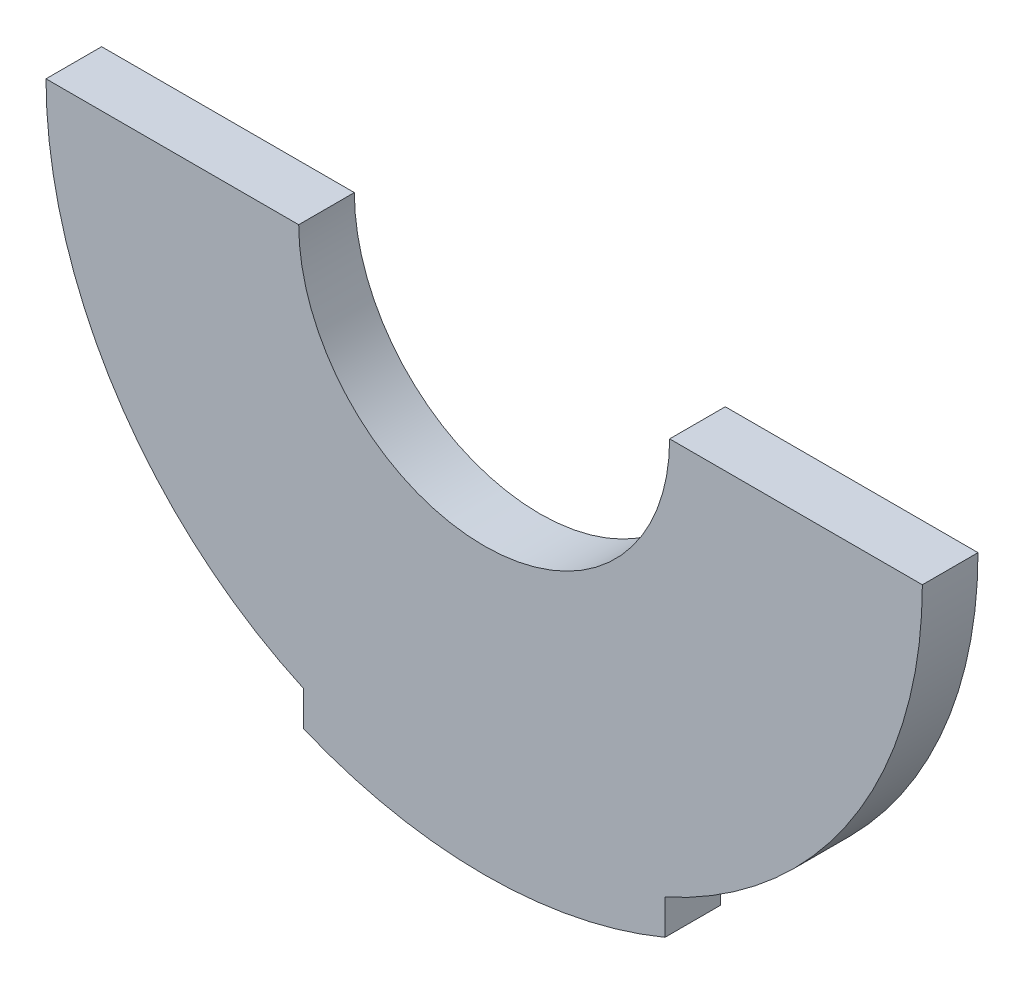
SolidWorks part; units mm, degrees
material "Perspex (TM) GS Acrylic Cast Sheet"
ref_plane "Front Plane" through (0, 0, 0) normal (0, 0, 1) x (1, 0, 0)
ref_plane "Top Plane" through (0, 0, 0) normal (0, 1, 0) x (1, 0, 0)
ref_plane "Right Plane" through (0, 0, 0) normal (1, 0, 0) x (0, 0, -1)
sketch "Sketch1" plane through (0, 0, 0) normal (0, 0, 1) x (1, 0, 0)
  line L0 (-47.25, 0) -> (-20, 0)
  line L1 (20, 0) -> (47.25, 0)
  line L2 (-19.5, -43.0385) -> (-19.5, -46.8)
  line L3 (19.5, -43.0385) -> (19.5, -46.8)
  arc A0 (-47.25, 0) -> (-19.5, -43.0385) centre (0, 0) ccw
  arc A1 (-20, 0) -> (20, 0) centre (0, 0) ccw
  arc A2 (-19.5, -46.8) -> (19.5, -46.8) centre (0, 0) ccw
  arc A3 (19.5, -43.0385) -> (47.25, 0) centre (0, 0) ccw
  dimension "D1" = 94.5
  dimension "D2" = 40
  dimension "D3" = 101.4
  dimension "D4" = 39
  dimension "D5" = 19.5
extrude "Boss-Extrude1" add sketch "Sketch1" along normal blind 6 contours L0 A1 L1 A3 L3 A2 L2 A0
